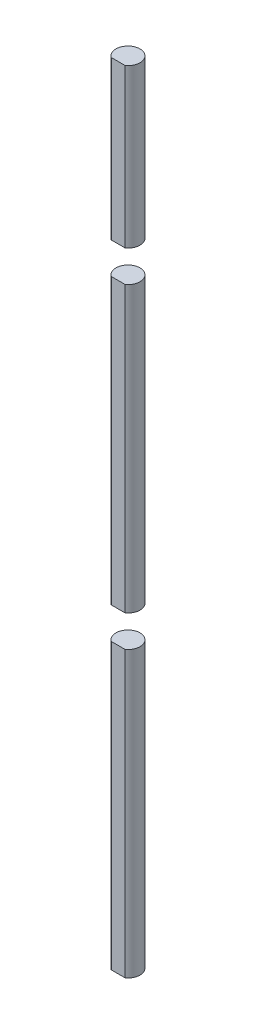
SolidWorks part; units mm, degrees
ref_plane "Front Plane" through (0, 0, 0) normal (0, 0, 1) x (1, 0, 0)
ref_plane "Top Plane" through (0, 0, 0) normal (0, 1, 0) x (1, 0, 0)
ref_plane "Right Plane" through (0, 0, 0) normal (1, 0, 0) x (0, 0, -1)
sketch "Sketch1" plane through (0, 0, 0) normal (0, 1, 0) x (1, 0, 0)
  line L0 (-1.0933, -1.5539) -> (1.0933, -1.5539)
  arc A0 (1.0933, -1.5539) -> (-1.0933, -1.5539) centre (0, 0) ccw
  dimension "D1" = 3.8
extrude "Boss-Extrude1" add sketch "Sketch1" along normal blind 130 contours A0 L0
ref_plane "Plane1" through (0, 0, 1.5539) normal (0, 0, 1) x (1, 0, 0)
sketch "Sketch2" plane through (0, 0, 1.5539) normal (0, 0, 1) x (1, 0, 0)
  line L1 (-1.0933, 130) -> (1.0933, 130)
  line L2 (-1.0933, 130) -> (-1.0933, 0)
  line L3 (-1.0933, 0) -> (1.0933, 0)
  line L4 (1.0933, 130) -> (1.0933, 0)
  line L5 (-8.2432, 45) -> (4.637, 45)
  line L6 (-8.2432, 45) -> (-8.2432, 50)
  line L7 (-8.2432, 50) -> (4.637, 50)
  line L8 (4.637, 45) -> (4.637, 50)
  line L9 (-9.5529, 100) -> (17.2753, 100)
  line L10 (-9.5529, 100) -> (-9.5529, 95)
  line L11 (-9.5529, 95) -> (17.2753, 95)
  line L12 (17.2753, 100) -> (17.2753, 95)
  line L13 (-6.3552, 130) -> (11.2578, 130)
  line L14 (-6.3552, 130) -> (-6.3552, 125)
  line L15 (-6.3552, 125) -> (11.2578, 125)
  line L16 (11.2578, 130) -> (11.2578, 125)
  dimension "D1" = 45
  dimension "D2" = 5
  dimension "D3" = 45
  dimension "D4" = 5
  dimension "D5" = 5
  dimension "D6" = 0
extrude "Cut-Extrude1" cut sketch "Sketch2" against normal blind 130 contours L16 L13 L4 L15 | L14 L15 L2 L13 | L2 L15 L4 L1 | L2 L11 L4 L9 | L10 L11 L2 L9 | L12 L9 L4 L11 | L7 L6 L5 L2 | L7 L2 L5 L4 | L5 L8 L7 L4
